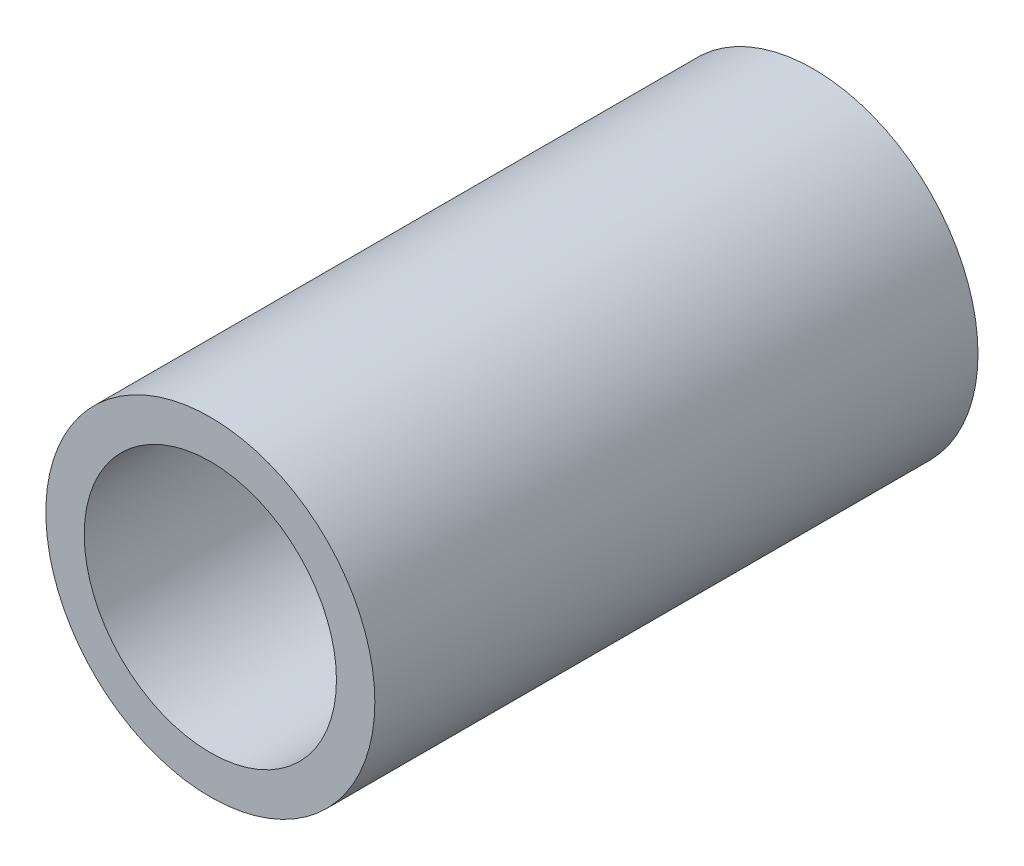
SolidWorks part; units mm, degrees
material "Nylon 101"
ref_plane "Front Plane" through (0, 0, 0) normal (0, 0, 1) x (1, 0, 0)
ref_plane "Top Plane" through (0, 0, 0) normal (0, 1, 0) x (1, 0, 0)
ref_plane "Right Plane" through (0, 0, 0) normal (1, 0, 0) x (0, 0, -1)
sketch "Sketch5" plane through (0, 0, 0) normal (0, 0, 1) x (1, 0, 0)
  circle A0 centre (0, 0) radius 30
  circle A1 centre (0, 0) radius 23
  dimension "D1" = 60
  dimension "D2" = 46
extrude "Boss-Extrude1" add sketch "Sketch5" along normal blind 110
